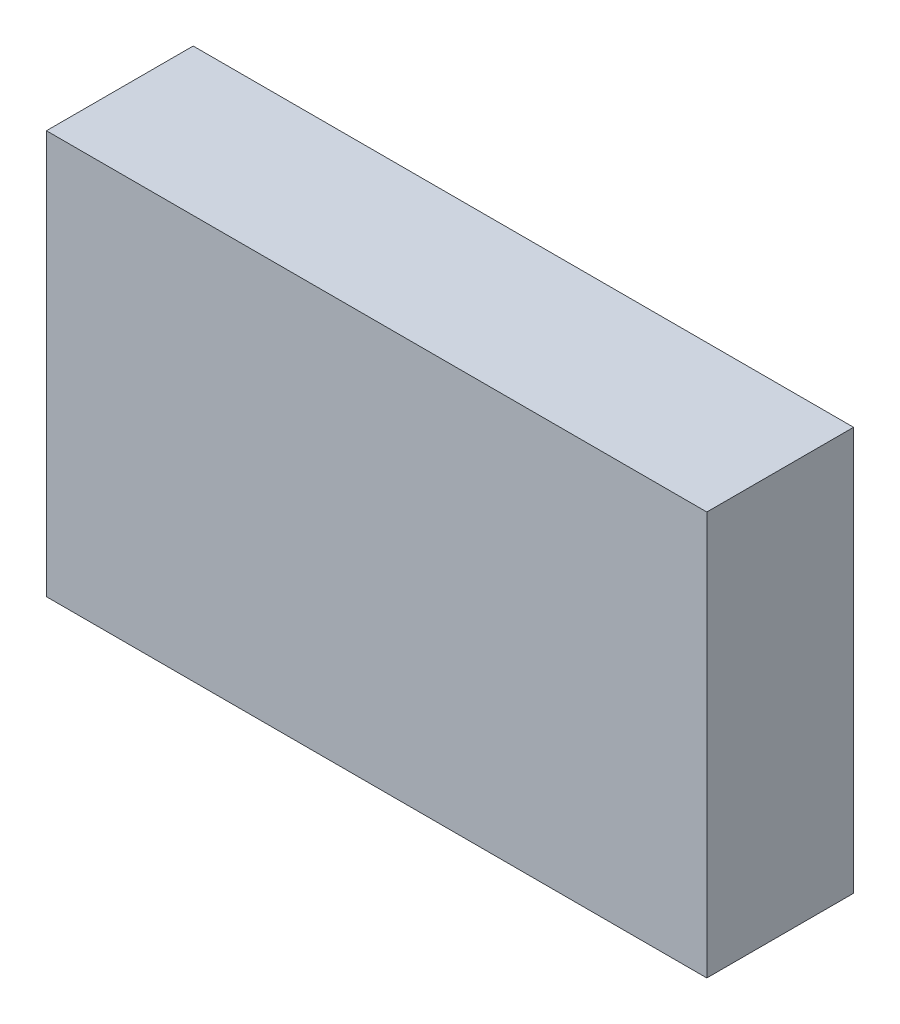
SolidWorks part; units mm, degrees
ref_plane "Спереди" through (0, 0, 0) normal (0, 0, 1) x (1, 0, 0)
ref_plane "Сверху" through (0, 0, 0) normal (0, 1, 0) x (1, 0, 0)
ref_plane "Справа" through (0, 0, 0) normal (1, 0, 0) x (0, 0, -1)
sketch "Эскиз1" plane through (0, 0, 0) normal (0, 0, 1) x (1, 0, 0)
  line L1 (0, 0) -> (-90, 0)
  line L2 (0, 0) -> (0, 55)
  line L3 (0, 55) -> (-90, 55)
  line L4 (-90, 0) -> (-90, 55)
  dimension "D1" = 90
  dimension "D2" = 55
extrude "Бобышка-Вытянуть1" add sketch "Эскиз1" along normal blind 20
